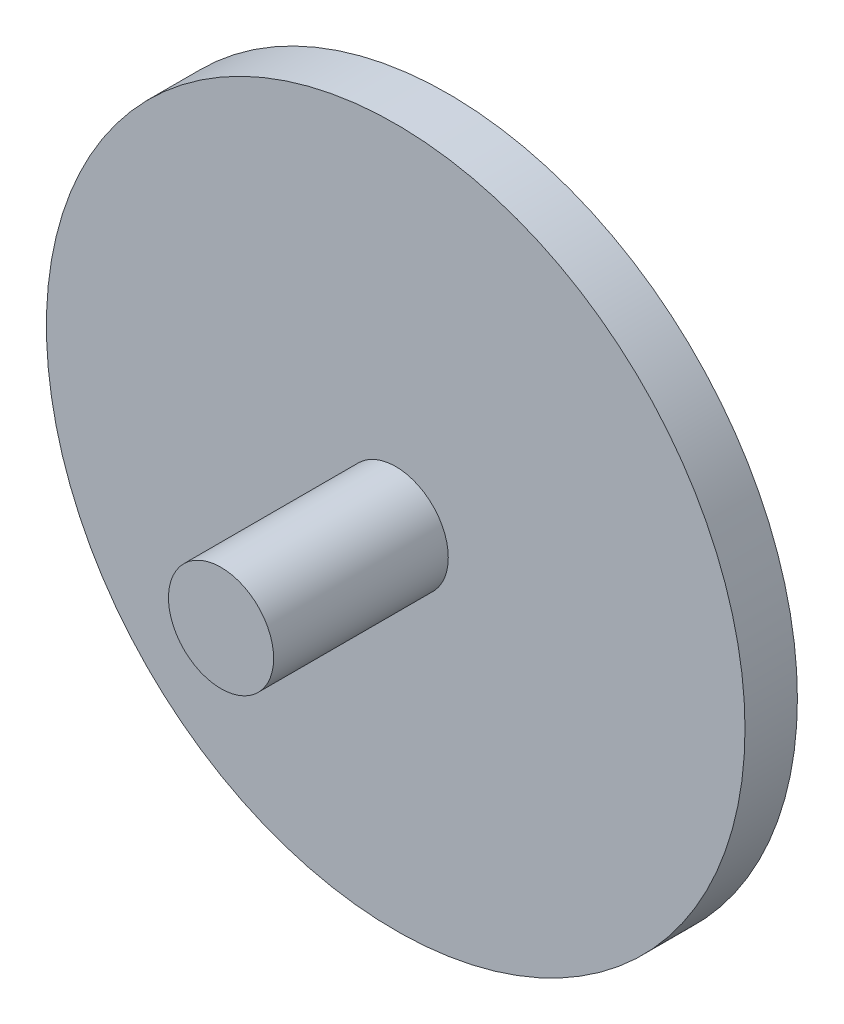
SolidWorks part; units mm, degrees
ref_plane "Alzado" through (0, 0, 0) normal (0, 0, 1) x (1, 0, 0)
ref_plane "Planta" through (0, 0, 0) normal (0, 1, 0) x (1, 0, 0)
ref_plane "Vista lateral" through (0, 0, 0) normal (1, 0, 0) x (0, 0, -1)
sketch "Croquis1" plane through (0, 0, 0) normal (0, 0, 1) x (1, 0, 0)
  circle A0 centre (0, 0) radius 10
  dimension "D1" = 20
sketch "Croquis2" plane through (0, 0, 0) normal (0, 0, 1) x (1, 0, 0)
extrude "Saliente-Extruir1" add sketch "Croquis1" along normal blind 1.5 contours A0
sketch "Croquis3" plane through (0, 0, 1.5) normal (0, 0, 1) x (1, 0, 0)
  circle A0 centre (0, 0) radius 1.5054
extrude "Saliente-Extruir2" add sketch "Croquis3" along normal blind 5
